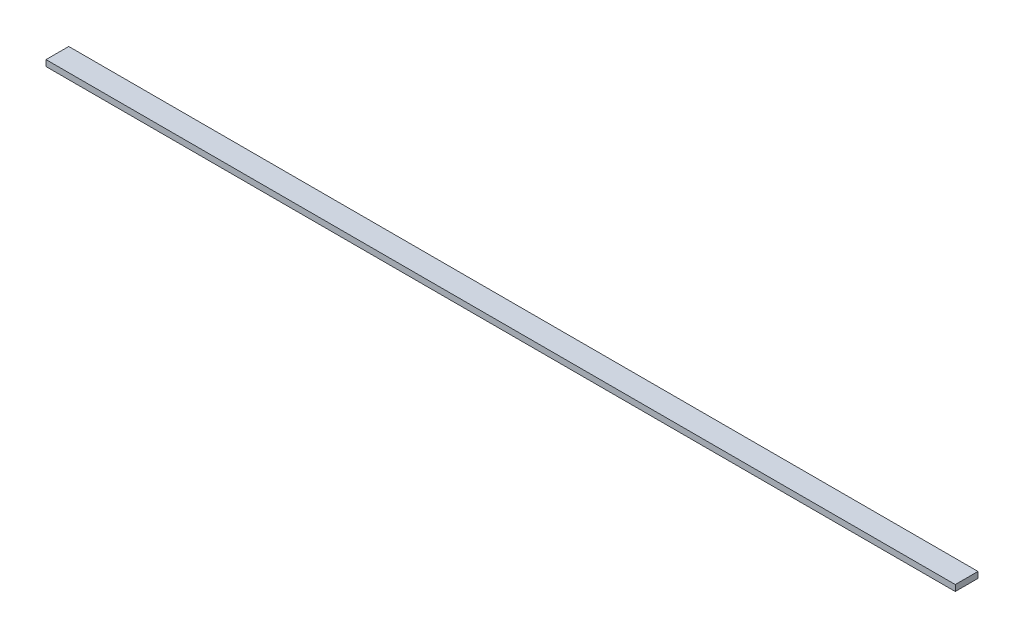
SolidWorks part; units mm, degrees
ref_plane "Спереди" through (0, 0, 0) normal (0, 0, 1) x (1, 0, 0)
ref_plane "Сверху" through (0, 0, 0) normal (0, 1, 0) x (1, 0, 0)
ref_plane "Справа" through (0, 0, 0) normal (1, 0, 0) x (0, 0, -1)
sketch "Эскиз1" plane through (0, 0, 0) normal (0, 1, 0) x (1, 0, 0)
  line L1 (-600, 15) -> (600, 15)
  line L2 (-600, 15) -> (-600, -15)
  line L3 (-600, -15) -> (600, -15)
  line L4 (600, 15) -> (600, -15)
  line L5 (-600, 15) -> (600, -15) construction
  line L6 (-600, -15) -> (600, 15) construction
  point P0 (0, 0)
extrude "Бобышка-Вытянуть1" add sketch "Эскиз1" along normal blind 8
